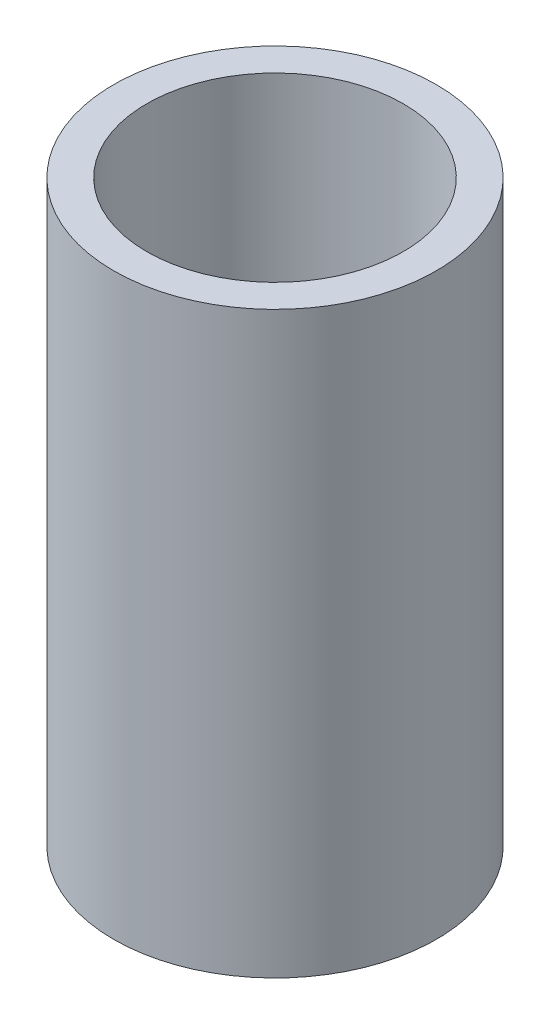
SolidWorks part; units mm, degrees
material "Acrylic (Medium-high impact)"
ref_plane "Front Plane" through (0, 0, 0) normal (0, 0, 1) x (1, 0, 0)
ref_plane "Top Plane" through (0, 0, 0) normal (0, 1, 0) x (1, 0, 0)
ref_plane "Right Plane" through (0, 0, 0) normal (1, 0, 0) x (0, 0, -1)
sketch "Sketch1" plane through (0, 0, 0) normal (0, 1, 0) x (1, 0, 0)
  circle A0 centre (0, 0) radius 9.75
  circle A1 centre (0, 0) radius 7.75
  dimension "D1" = 15.5
  dimension "D2" = 19.5
extrude "Boss-Extrude1" add sketch "Sketch1" along normal blind 35
